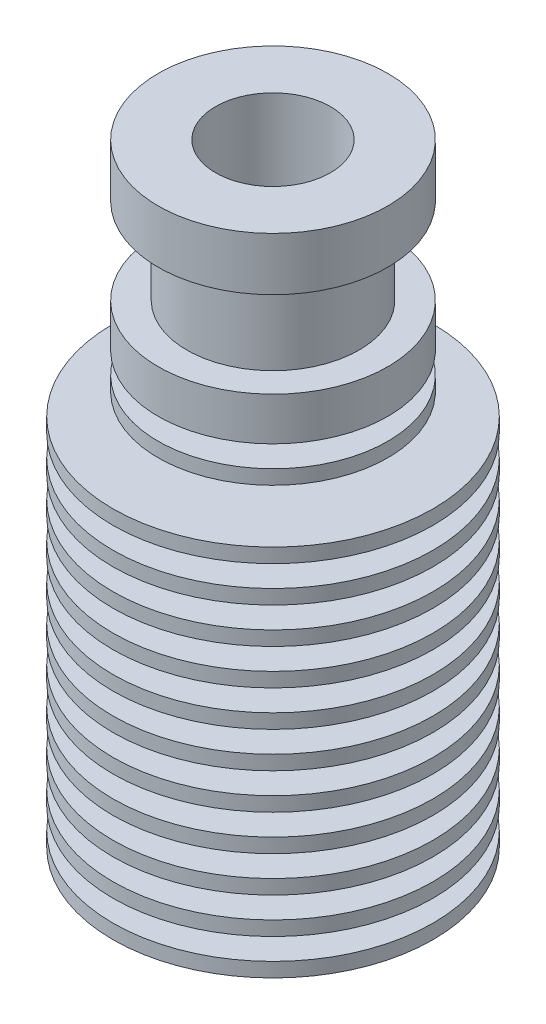
SolidWorks part; units mm, degrees
material "1060 Alloy"
ref_plane "Front Plane" through (0, 0, 0) normal (0, 0, 1) x (1, 0, 0)
ref_plane "Top Plane" through (0, 0, 0) normal (0, 1, 0) x (1, 0, 0)
ref_plane "Right Plane" through (0, 0, 0) normal (1, 0, 0) x (0, 0, -1)
sketch "Sketch1" plane through (0, 0, 0) normal (0, 0, 1) x (1, 0, 0)
  line L0 (11.15, 18.5) -> (5.0829, 18.5)
  line L1 (5.0829, 18.5) -> (5.0829, 20)
  line L2 (5.0829, 20) -> (11.15, 20)
  line L3 (11.15, 20) -> (11.15, 21)
  line L4 (11.15, 21) -> (4.9518, 21)
  line L5 (4.9518, 21) -> (4.9518, 22.5)
  line L6 (4.9518, 22.5) -> (11.15, 22.5)
  line L7 (11.15, 22.5) -> (11.15, 23.5)
  line L8 (11.15, 23.5) -> (4.8208, 23.5)
  line L9 (4.8208, 23.5) -> (4.8208, 25)
  line L10 (4.8208, 25) -> (11.15, 25)
  line L11 (11.15, 25) -> (11.15, 26)
  line L12 (11.15, 26) -> (4.6898, 26)
  line L13 (4.6898, 26) -> (4.6898, 27.5)
  line L14 (4.6898, 27.5) -> (8, 27.5)
  line L15 (8, 27.5) -> (8, 28.5)
  line L16 (8, 28.5) -> (4.6898, 28.5)
  line L17 (4.6898, 28.5) -> (4.6898, 30)
  line L18 (4.6898, 30) -> (8, 30)
  line L19 (8, 30) -> (8, 33)
  line L20 (8, 33) -> (6, 33)
  line L21 (6, 33) -> (6, 39)
  line L22 (6, 39) -> (8, 39)
  line L23 (8, 39) -> (8, 42.7)
  line L24 (8, 42.7) -> (4, 42.7)
  line L25 (4, 42.7) -> (4, 36.6)
  line L26 (4, 36.6) -> (2.1, 34.7)
  line L27 (2.1, 34.7) -> (2.1, 14.7)
  line L28 (2.1, 14.7) -> (3.5, 13.3)
  line L29 (3.5, 13.3) -> (3.5, 0)
  line L30 (3.5, 0) -> (11.15, 0)
  line L31 (11.15, 0) -> (11.15, 1)
  line L32 (11.15, 1) -> (6, 1)
  line L33 (6, 1) -> (6, 2.5)
  line L34 (6, 2.5) -> (11.15, 2.5)
  line L35 (11.15, 2.5) -> (11.15, 3.5)
  line L36 (11.15, 3.5) -> (5.869, 3.5)
  line L37 (5.869, 3.5) -> (5.869, 5)
  line L38 (5.869, 5) -> (11.15, 5)
  line L39 (11.15, 5) -> (11.15, 6)
  line L40 (11.15, 6) -> (5.738, 6)
  line L41 (5.738, 6) -> (5.738, 7.5)
  line L42 (5.738, 7.5) -> (11.15, 7.5)
  line L43 (11.15, 7.5) -> (11.15, 8.5)
  line L44 (11.15, 8.5) -> (5.6069, 8.5)
  line L45 (5.6069, 8.5) -> (5.6069, 10)
  line L46 (5.6069, 10) -> (11.15, 10)
  line L47 (11.15, 10) -> (11.15, 11)
  line L48 (11.15, 11) -> (5.4759, 11)
  line L49 (5.4759, 11) -> (5.4759, 12.5)
  line L50 (5.4759, 12.5) -> (11.15, 12.5)
  line L51 (11.15, 12.5) -> (11.15, 13.5)
  line L52 (11.15, 13.5) -> (5.3449, 13.5)
  line L53 (5.3449, 13.5) -> (5.3449, 15)
  line L54 (5.3449, 15) -> (11.15, 15)
  line L55 (11.15, 15) -> (11.15, 16)
  line L56 (11.15, 16) -> (5.2139, 16)
  line L57 (5.2139, 16) -> (5.2139, 17.5)
  line L58 (5.2139, 17.5) -> (11.15, 17.5)
  line L59 (11.15, 17.5) -> (11.15, 18.5)
  line L60 (0, 42.7) -> (0, 0) construction
revolve "Revolve1" add sketch "Sketch1" angle 360 about L60
